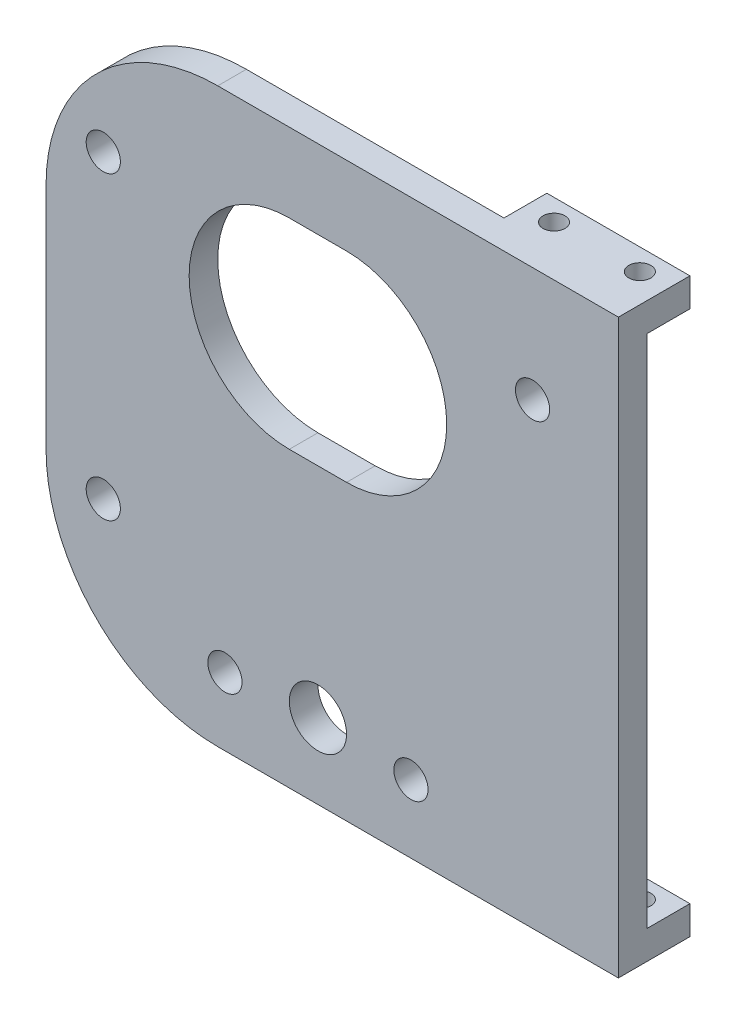
SolidWorks part; units mm, degrees
material "Polycarbonate"
ref_plane "Front Plane" through (0, 0, 0) normal (0, 0, 1) x (1, 0, 0)
ref_plane "Top Plane" through (0, 0, 0) normal (0, 1, 0) x (1, 0, 0)
ref_plane "Right Plane" through (0, 0, 0) normal (1, 0, 0) x (0, 0, -1)
sketch "Sketch1" plane through (0, 0, 0) normal (0, 0, 1) x (1, 0, 0)
  line L1 (-31.75, 31.75) -> (31.75, 31.75)
  line L2 (-31.75, 31.75) -> (-31.75, -31.75)
  line L3 (-31.75, -31.75) -> (31.75, -31.75)
  line L4 (31.75, 31.75) -> (31.75, -31.75)
  line L5 (-31.75, 31.75) -> (31.75, -31.75) construction
  line L6 (-31.75, -31.75) -> (31.75, 31.75) construction
  point P0 (0, 0)
  dimension "D1" = 63.5
  dimension "D2" = 63.5
extrude "Boss-Extrude1" add sketch "Sketch1" along normal blind 3.175
sketch "Sketch2" plane through (0, 0, 0) normal (0, 0, -1) x (-1, 0, 0)
  line L0 (31.75, -31.75) -> (-31.75, -31.75) construction
  line L1 (-25.4, -31.75) -> (-15.875, -31.75)
  line L3 (-25.4, -28.575) -> (-15.875, -28.575)
  line L4 (-15.875, -31.75) -> (-15.875, -28.575)
  line L5 (-31.75, -31.75) -> (-31.75, 31.75) construction
  line L7 (-31.75, -31.75) -> (-25.4, -31.75)
  line L8 (-31.75, -31.75) -> (-31.75, -28.575)
  line L9 (-31.75, -28.575) -> (-25.4, -28.575)
  dimension "D1" = 3.175
  dimension "D2" = 15.875
  dimension "D4" = 6.35
extrude "Boss-Extrude2" add sketch "Sketch2" along normal blind 4.7625
hole_wizard "#2 Clearance Hole1" positions "Sketch3" profile "Sketch4" hole size "#2" standard "ANSI Inch" end condition up to next
sketch "Sketch3" plane through (0, -28.575, 0) normal (0, 1, 0) x (1, 0, 0)
  line L0 (15.875, 4.7625) -> (15.875, 0) construction
  line L6 (31.75, 4.7625) -> (31.75, 0) construction
  point P0 (28.575, 2.3813)
  point P5 (15.875, 2.3813)
  point P21 (19.05, 2.3813)
  dimension "D1" = 3.175
  dimension "D2" = 3.175
sketch "Sketch4" plane through (28.575, -28.575, -2.3813) normal (1, 0, 0) x (0, 0, 1)
  line L0 (0, 0) -> (0, 3.175)
  line L1 (0, 3.175) -> (1.2192, 3.175)
  line L2 (1.2192, 3.175) -> (1.2192, 0)
  line L5 (1.2192, 0) -> (0, 0)
  line L11 (0, -6.35) -> (0, 107.95) construction
  dimension "Thru Hole Dia." = 2.4384
  dimension "Thru Hole Depth" = 3.175
fillet "Fillet1" radius 19.05 2 edges at (-31.75, -31.75, 1.5875) (-31.75, 31.75, 1.5875)
sketch "Sketch5" plane through (0, 0, 0) normal (0, 0, -1) x (-1, 0, 0)
  line L0 (-15.875, -31.75) -> (-15.875, -28.575) construction
  line L1 (-31.75, 31.75) -> (-15.875, 31.75)
  line L2 (-31.75, 31.75) -> (-31.75, 28.575)
  line L3 (-31.75, 28.575) -> (-15.875, 28.575)
  line L4 (-15.875, 31.75) -> (-15.875, 28.575)
  dimension "D1" = 3.175
extrude "Boss-Extrude3" add sketch "Sketch5" along normal blind 4.7625
hole_wizard "#2 Clearance Hole2" positions "Sketch6" profile "Sketch7" hole size "#2" standard "ANSI Inch" end condition up to next
sketch "Sketch6" plane through (0, 28.575, 0) normal (0, -1, 0) x (-1, 0, 0)
  point P0 (-19.05, 2.3813)
  point P3 (-28.575, 2.3813)
sketch "Sketch7" plane through (19.05, 28.575, -2.3813) normal (1, 0, 0) x (0, 0, -1)
  line L0 (0, 0) -> (0, 3.175)
  line L1 (0, 3.175) -> (1.2192, 3.175)
  line L2 (1.2192, 3.175) -> (1.2192, 0)
  line L5 (1.2192, 0) -> (0, 0)
  line L11 (0, -6.35) -> (0, 107.95) construction
  dimension "Thru Hole Dia." = 2.4384
  dimension "Thru Hole Depth" = 3.175
sketch "Sketch8" plane through (0, 0, 3.175) normal (0, 0, 1) x (1, 0, 0)
  line L0 (-25.4, 19.05) -> (-25.4, -14.2875) construction
  line L1 (-25.4, -14.2875) -> (-11.9062, -24.2094) construction
  line L2 (-11.9062, -24.2094) -> (8.7313, -24.2094) construction
  line L3 (8.7313, -24.2094) -> (22.225, -24.2094) construction
  line L4 (22.225, -24.2094) -> (22.225, 19.05) construction
  line L5 (22.225, 19.05) -> (-25.4, 19.05) construction
  line L6 (-12.7, -31.75) -> (31.75, -31.75) construction
  line L7 (31.75, -31.75) -> (31.75, 31.75) construction
  circle A0 centre (-25.4, 19.05) radius 3.175
  circle A1 centre (-25.4, -14.2875) radius 3.175
  circle A2 centre (22.225, 19.05) radius 3.175
  circle A3 centre (8.7313, -24.2094) radius 3.175
  circle A4 centre (-11.9062, -24.2094) radius 3.175
  dimension "D8" = 6.35
  dimension "D1" = 33.3375
  dimension "D2" = 47.625
  dimension "D3" = 43.2594
  dimension "D4" = 13.4937
  dimension "D5" = 20.6375
  dimension "D6" = 7.5406
  dimension "D7" = 9.525
extrude "Boss-Extrude4" add sketch "Sketch8" against normal blind 3.175 from surface at -3.175 starting at face at (3.0209, 0, 0)
hole_wizard "#6 Clearance Hole1" positions "Sketch9" profile "Sketch10" hole size "#6" standard "ANSI Inch" end condition through all
sketch "Sketch9" plane through (0, 0, -3.175) normal (0, 0, -1) x (-1, 0, 0)
  point P0 (-22.225, 19.05)
  point P3 (25.4, 19.05)
  point P6 (25.4, -14.2875)
  point P9 (11.9062, -24.2094)
  point P12 (-8.7313, -24.2094)
sketch "Sketch10" plane through (22.225, 19.05, -3.175) normal (1, 0, 0) x (0, 1, 0)
  line L0 (0, 0) -> (0, 6.35)
  line L1 (0, 6.35) -> (1.8986, 6.35)
  line L2 (1.8986, 6.35) -> (1.8986, 0)
  line L5 (1.8986, 0) -> (0, 0)
  line L11 (0, -6.35) -> (0, 107.95) construction
  dimension "Thru Hole Dia." = 3.7973
  dimension "Thru Hole Depth" = 6.35
sketch "Sketch11" plane through (0, 0, 3.175) normal (0, 0, 1) x (1, 0, 0)
  line L0 (-25.4, 19.05) -> (22.225, 19.05) construction
  line L1 (-15.875, 23.0188) -> (12.7, 23.0188) construction
  line L2 (-15.875, 23.0188) -> (-15.875, 0.7938) construction
  line L3 (-15.875, 0.7938) -> (12.7, 0.7938) construction
  line L4 (12.7, 23.0188) -> (12.7, 0.7938) construction
  line L5 (31.75, 31.75) -> (-12.7, 31.75) construction
  line L6 (-4.7625, 11.9063) -> (1.5875, 11.9063) construction
  line L7 (-4.7625, 23.0188) -> (1.5875, 23.0188)
  line L8 (-4.7625, 0.7938) -> (1.5875, 0.7938)
  circle A0 centre (22.225, 19.05) radius 1.8986 construction
  circle A1 centre (-25.4, 19.05) radius 1.8986 construction
  circle A2 centre (22.225, 19.05) radius 1.8986 construction
  circle A3 centre (-25.4, 19.05) radius 1.8986 construction
  arc A5 (-4.7625, 23.0188) -> (-4.7625, 0.7938) centre (-4.7625, 11.9063) ccw
  arc A6 (1.5875, 0.7938) -> (1.5875, 23.0188) centre (1.5875, 11.9063) ccw
  circle A7 centre (-1.5875, -23.4156) radius 3.175
  circle A8 centre (8.7313, -24.2094) radius 1.8986 construction
  circle A9 centre (-11.9062, -24.2094) radius 1.8986 construction
  circle A10 centre (8.7313, -24.2094) radius 1.8986 construction
  circle A11 centre (-11.9062, -24.2094) radius 1.8986 construction
  point P10 (-1.5875, 19.05)
  point P11 (-1.5875, 23.0188)
  point P17 (-1.5875, 11.9063)
  point P19 (-15.875, 11.9063)
  point P27 (-1.5875, 23.0188)
  point P28 (-1.5875, 0.7938)
  dimension "D5" = 6.35
  dimension "D1" = 28.575
  dimension "D2" = 22.225
  dimension "D3" = 8.7312
  dimension "D4" = 0.7937
extrude "Cut-Extrude1" cut sketch "Sketch11" against normal up to next
